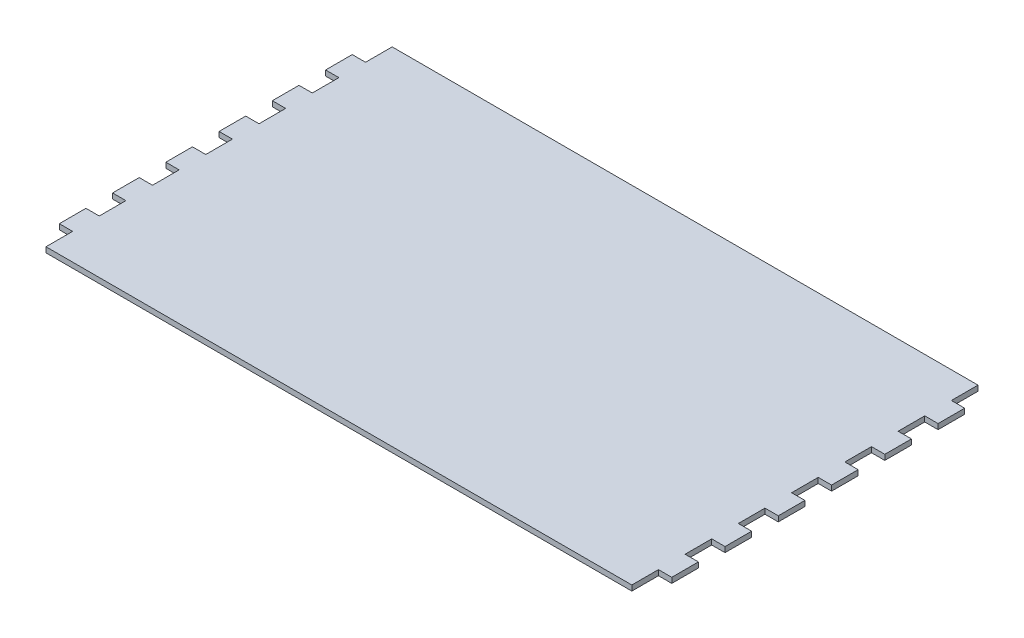
SolidWorks part; units mm, degrees
ref_plane "Front Plane" through (0, 0, 0) normal (0, 0, 1) x (1, 0, 0)
ref_plane "Top Plane" through (0, 0, 0) normal (0, 1, 0) x (1, 0, 0)
ref_plane "Right Plane" through (0, 0, 0) normal (1, 0, 0) x (0, 0, -1)
sketch "Sketch1" plane through (0, 0, 0) normal (0, 1, 0) x (1, 0, 0)
  line L0 (0, 0) -> (279.4, 0)
  line L1 (0, 0) -> (0, -12.7)
  line L2 (0, -12.7) -> (-6.35, -12.7)
  line L3 (-6.35, -12.7) -> (-6.35, -25.4)
  line L4 (-6.35, -25.4) -> (0, -25.4)
  line L5 (0, -25.4) -> (0, -38.1)
  line L6 (0, -38.1) -> (-6.35, -38.1)
  line L7 (-6.35, -38.1) -> (-6.35, -50.8)
  line L8 (-6.35, -50.8) -> (0, -50.8)
  line L9 (0, -50.8) -> (0, -63.5)
  line L10 (0, -63.5) -> (-6.35, -63.5)
  line L11 (-6.35, -63.5) -> (-6.35, -76.2)
  line L12 (-6.35, -76.2) -> (0, -76.2)
  line L13 (0, -76.2) -> (0, -88.9)
  line L14 (0, -88.9) -> (-6.35, -88.9)
  line L15 (-6.35, -88.9) -> (-6.35, -101.6)
  line L16 (-6.35, -101.6) -> (0, -101.6)
  line L17 (0, -101.6) -> (0, -114.3)
  line L18 (0, -114.3) -> (-6.35, -114.3)
  line L19 (-6.35, -114.3) -> (-6.35, -127)
  line L20 (-6.35, -127) -> (0, -127)
  line L21 (0, -127) -> (0, -139.7)
  line L22 (0, -139.7) -> (-6.35, -139.7)
  line L23 (-6.35, -139.7) -> (-6.35, -152.4)
  line L24 (-6.35, -152.4) -> (0, -152.4)
  line L25 (0, -152.4) -> (0, -165.1)
  line L26 (139.7, 0) -> (139.7, -165.1) construction
  line L27 (279.4, -152.4) -> (279.4, -165.1)
  line L28 (285.75, -152.4) -> (279.4, -152.4)
  line L29 (285.75, -139.7) -> (285.75, -152.4)
  line L30 (279.4, -139.7) -> (285.75, -139.7)
  line L31 (279.4, -127) -> (279.4, -139.7)
  line L32 (285.75, -127) -> (279.4, -127)
  line L33 (285.75, -114.3) -> (285.75, -127)
  line L34 (279.4, -114.3) -> (285.75, -114.3)
  line L35 (279.4, -101.6) -> (279.4, -114.3)
  line L36 (285.75, -101.6) -> (279.4, -101.6)
  line L37 (285.75, -88.9) -> (285.75, -101.6)
  line L38 (279.4, -88.9) -> (285.75, -88.9)
  line L39 (279.4, -76.2) -> (279.4, -88.9)
  line L40 (285.75, -76.2) -> (279.4, -76.2)
  line L41 (285.75, -63.5) -> (285.75, -76.2)
  line L42 (279.4, -63.5) -> (285.75, -63.5)
  line L43 (279.4, -50.8) -> (279.4, -63.5)
  line L44 (285.75, -50.8) -> (279.4, -50.8)
  line L45 (285.75, -38.1) -> (285.75, -50.8)
  line L46 (279.4, -38.1) -> (285.75, -38.1)
  line L47 (279.4, -25.4) -> (279.4, -38.1)
  line L48 (285.75, -25.4) -> (279.4, -25.4)
  line L49 (285.75, -12.7) -> (285.75, -25.4)
  line L50 (279.4, -12.7) -> (285.75, -12.7)
  line L51 (279.4, 0) -> (279.4, -12.7)
  line L52 (0, -165.1) -> (279.4, -165.1)
  dimension "D1" = 12.7
  dimension "D2" = 12.7
  dimension "D3" = 6.35
  dimension "D4" = 6.35
  dimension "D5" = 279.4
  dimension "D7" = 12.7
  dimension "D6" = 6
extrude "Boss-Extrude1" add sketch "Sketch1" along normal blind 2.54
